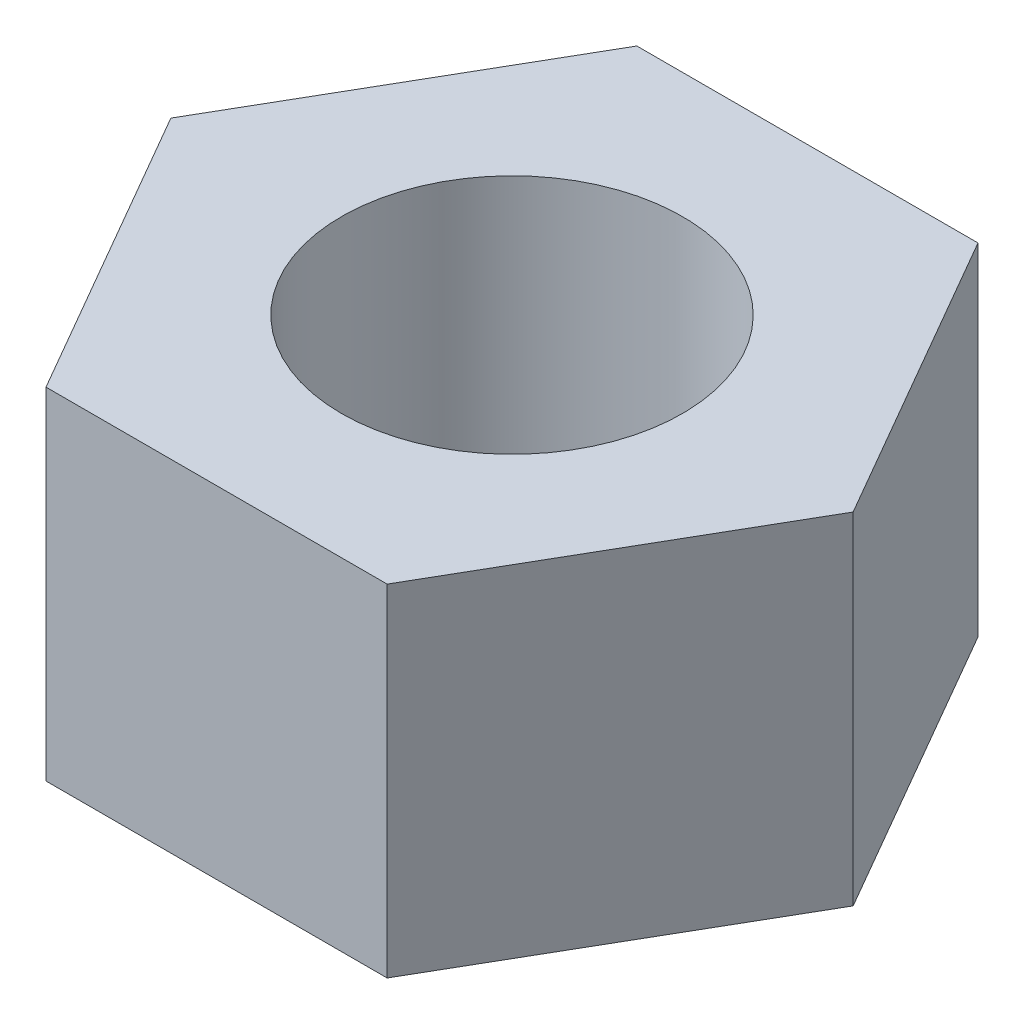
SolidWorks part; units mm, degrees
ref_plane "Front Plane" through (0, 0, 0) normal (0, 0, 1) x (1, 0, 0)
ref_plane "Top Plane" through (0, 0, 0) normal (0, 1, 0) x (1, 0, 0)
ref_plane "Right Plane" through (0, 0, 0) normal (1, 0, 0) x (0, 0, -1)
sketch "Sketch1" plane through (0, 0, 0) normal (0, 1, 0) x (1, 0, 0)
  line L1 (4.5, -7.7942) -> (9, 0)
  line L2 (9, 0) -> (4.5, 7.7942)
  line L3 (4.5, 7.7942) -> (-4.5, 7.7942)
  line L4 (-4.5, 7.7942) -> (-9, 0)
  line L5 (-9, 0) -> (-4.5, -7.7942)
  line L6 (-4.5, -7.7942) -> (4.5, -7.7942)
  circle A0 centre (0, 0) radius 7.7942 construction
  circle A1 centre (0, 0) radius 4.5
  dimension "D1" = 9
  dimension "D2" = 9
extrude "Boss-Extrude1" add sketch "Sketch1" along normal mid plane 9
